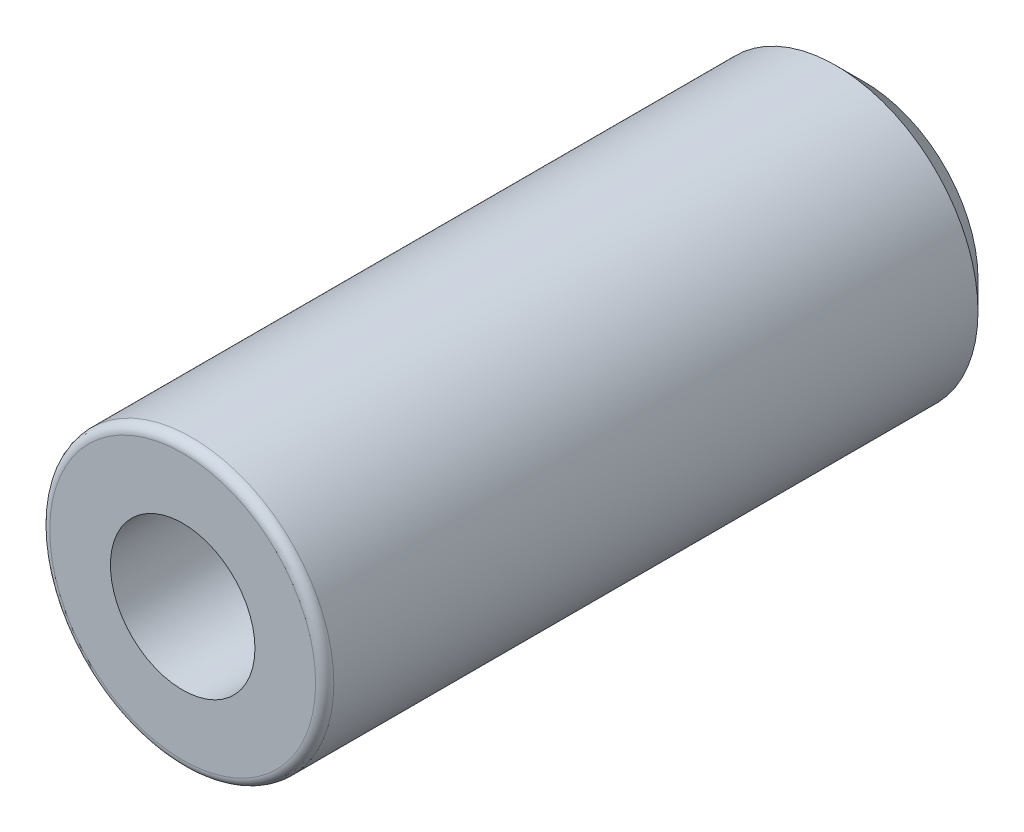
SolidWorks part; units mm, degrees
material "SS 304 (Default)"
ref_plane "Front Plane" through (0, 0, 0) normal (0, 0, 1) x (1, 0, 0)
ref_plane "Top Plane" through (0, 0, 0) normal (0, 1, 0) x (1, 0, 0)
ref_plane "Right Plane" through (0, 0, 0) normal (1, 0, 0) x (0, 0, -1)
sketch "Sketch1" plane through (0, 0, 0) normal (0, 0, 1) x (1, 0, 0)
  circle A0 centre (0, 0) radius 3.9688
  dimension "D1" = 7.9375
extrude "Extrude1" add sketch "Sketch1" along normal mid plane 19.05
sketch "Sketch2" plane through (0, 0, 0) normal (1, 0, 0) x (0, 0, -1)
  line L0 (9.525, 3.9688) -> (-9.525, 3.9688) construction
  line L1 (-6.2992, 3.9687) -> (-7.0358, 3.9687)
  line L2 (-7.0358, 3.9687) -> (-7.0358, 2.921)
  line L3 (-7.0358, 2.921) -> (-6.2992, 2.921)
  line L4 (-6.2992, 2.921) -> (-6.2992, 3.9687)
  line L5 (-9.525, 3.9688) -> (-9.525, -3.9688) construction
  line L6 (-9.525, 0) -> (9.525, 0) construction
  dimension "D1" = 2.4892
  dimension "D2" = 0.7366
  dimension "D3" = 2.921
revolve "Cut-Revolve1" [suppressed] cut sketch "Sketch2" angle 360
fillet "Fillet1" radius 0.254 1 edges at (3.9688, 0, 9.525)
chamfer "Chamfer1" distance 0.7937 angle 45 1 edges at (3.9688, 0, -9.525)
hole_wizard "#10-32 Tapped Hole1" positions "Sketch3" profile "Sketch4" tap size "#10-32" standard "ANSI Inch"
sketch "Sketch3" plane through (0, 0, 9.525) normal (0, 0, 1) x (1, 0, 0)
  point P0 (0, 0)
sketch "Sketch4" plane through (0, 0, 9.525) normal (1, 0, 0) x (0, -1, 0)
  line L0 (0, 0) -> (0, 13.2529)
  line L1 (0, 13.2529) -> (2.0193, 12.0396)
  line L2 (2.0193, 12.0396) -> (2.0193, 0)
  line L5 (2.0193, 0) -> (0, 0)
  line L10 (0, 13.2529) -> (-2.0193, 12.0396) construction
  line L11 (0, -6.35) -> (0, 107.95) construction
  dimension "Tap Drill Dia." = 4.0386
  dimension "Tap Drill Depth" = 12.0396
  dimension "Drill Angle" = 118
cosmetic thread "Hole Thread1" parameters "D1"=9.652, "D2"=4.826
